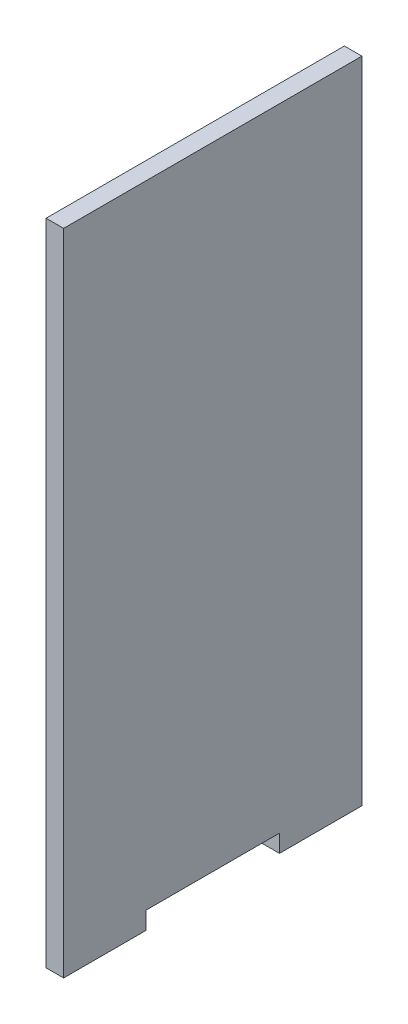
SolidWorks part; units mm, degrees
ref_plane "Front Plane" through (0, 0, 0) normal (0, 0, 1) x (1, 0, 0)
ref_plane "Top Plane" through (0, 0, 0) normal (0, 1, 0) x (1, 0, 0)
ref_plane "Right Plane" through (0, 0, 0) normal (1, 0, 0) x (0, 0, -1)
sketch "Sketch1" plane through (0, 0, 0) normal (1, 0, 0) x (0, 0, -1)
  line L0 (0, 0) -> (0, 180) construction
  line L1 (-42.5, 180) -> (42.5, 180)
  line L2 (-42.5, 180) -> (-42.5, 0)
  line L3 (-19, 0) -> (19, 0)
  line L4 (42.5, 180) -> (42.5, 0)
  line L5 (-42.5, 0) -> (-42.5, -5)
  line L6 (-42.5, -5) -> (-19, -5)
  line L7 (-19, -5) -> (-19, 0)
  line L8 (19, -5) -> (19, 0)
  line L9 (42.5, -5) -> (19, -5)
  line L10 (42.5, 0) -> (42.5, -5)
  line L11 (-42.5, 0) -> (-19, 0) construction
  line L12 (19, 0) -> (42.5, 0) construction
  dimension "D1" = 85
  dimension "D2" = 180
  dimension "D3" = 5
  dimension "D4" = 23.5
  dimension "D5" = 38
extrude "Boss-Extrude1" add sketch "Sketch1" along normal blind 5
